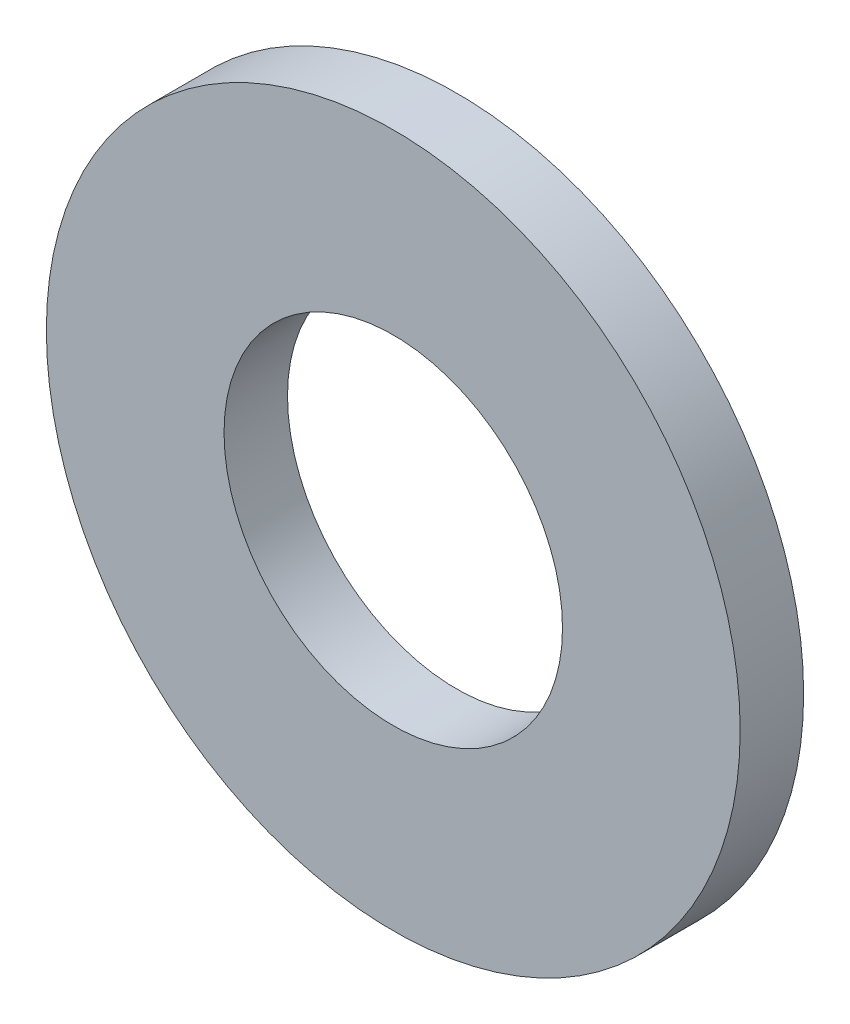
SolidWorks part; units mm, degrees
ref_plane "Front Plane" through (0, 0, 0) normal (0, 0, 1) x (1, 0, 0)
ref_plane "Top Plane" through (0, 0, 0) normal (0, 1, 0) x (1, 0, 0)
ref_plane "Right Plane" through (0, 0, 0) normal (1, 0, 0) x (0, 0, -1)
sketch "Sketch1" plane through (0, 0, 0) normal (0, 0, 1) x (1, 0, 0)
  circle A0 centre (0, 0) radius 10.414
  circle A1 centre (0, 0) radius 5.08
  dimension "D1" = 20.828
  dimension "D2" = 10.16
extrude "Boss-Extrude1" add sketch "Sketch1" along normal blind 1.905
